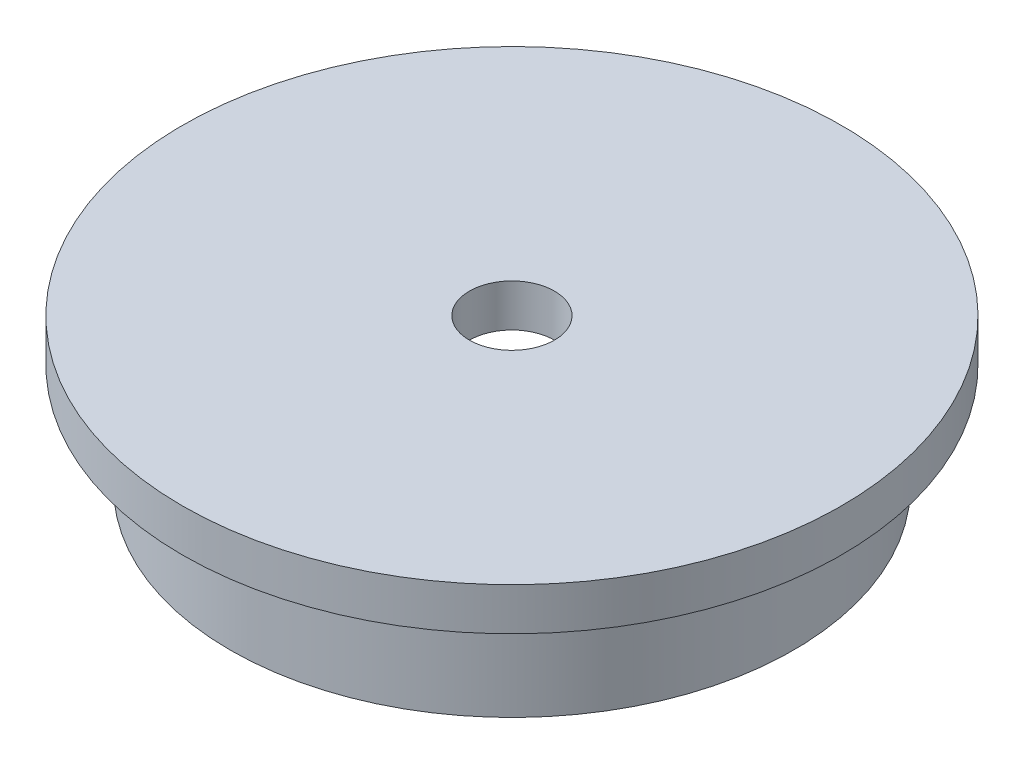
SolidWorks part; units mm, degrees
ref_plane "Front Plane" through (0, 0, 0) normal (0, 0, 1) x (1, 0, 0)
ref_plane "Top Plane" through (0, 0, 0) normal (0, 1, 0) x (1, 0, 0)
ref_plane "Right Plane" through (0, 0, 0) normal (1, 0, 0) x (0, 0, -1)
sketch "Sketch1" plane through (0, 0, 0) normal (0, 1, 0) x (1, 0, 0)
  circle A0 centre (0, 0) radius 33.655
  circle A1 centre (0, 0) radius 28.575
  dimension "D1" = 67.31
  dimension "D2" = 5.08
extrude "Boss-Extrude1" add sketch "Sketch1" along normal blind 12.7
sketch "Sketch2" plane through (0, 12.7, 0) normal (0, 1, 0) x (1, 0, 0)
  circle A1 centre (0, 0) radius 39.37
  dimension "D1" = 78.74
extrude "Boss-Extrude2" add sketch "Sketch2" along normal blind 5.08
sketch "Sketch3" plane through (0, 17.78, 0) normal (0, 1, 0) x (1, 0, 0)
  circle A0 centre (0, 0) radius 5.08
  dimension "D1" = 10.16
extrude "Cut-Extrude1" cut sketch "Sketch3" against normal through all both and the other way through all
